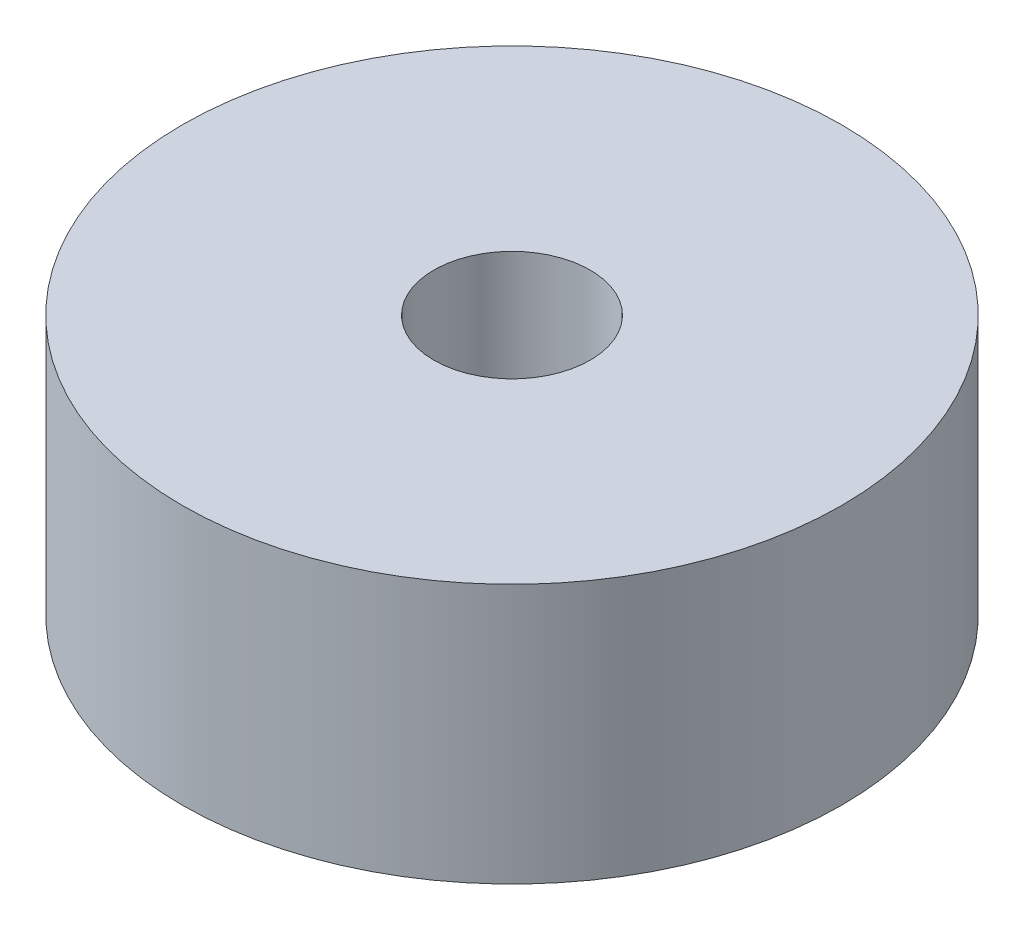
SolidWorks part; units mm, degrees
material "Natural Rubber"
ref_plane "Front Plane" through (0, 0, 0) normal (0, 0, 1) x (1, 0, 0)
ref_plane "Top Plane" through (0, 0, 0) normal (0, 1, 0) x (1, 0, 0)
ref_plane "Right Plane" through (0, 0, 0) normal (1, 0, 0) x (0, 0, -1)
sketch "Sketch1" plane through (0, 0, 0) normal (0, 1, 0) x (1, 0, 0)
  circle A0 centre (0, 0) radius 63.5
  dimension "D1" = 127
extrude "Boss-Extrude1" add sketch "Sketch1" along normal blind 50
sketch "Sketch2" plane through (0, 50, 0) normal (0, 1, 0) x (1, 0, 0)
  circle A0 centre (0, 0) radius 15.05
  dimension "D1" = 30.1
extrude "Cut-Extrude1" cut sketch "Sketch2" against normal up to surface (50 mm away) contours A0 up to face at (0, 0, 63.5)
